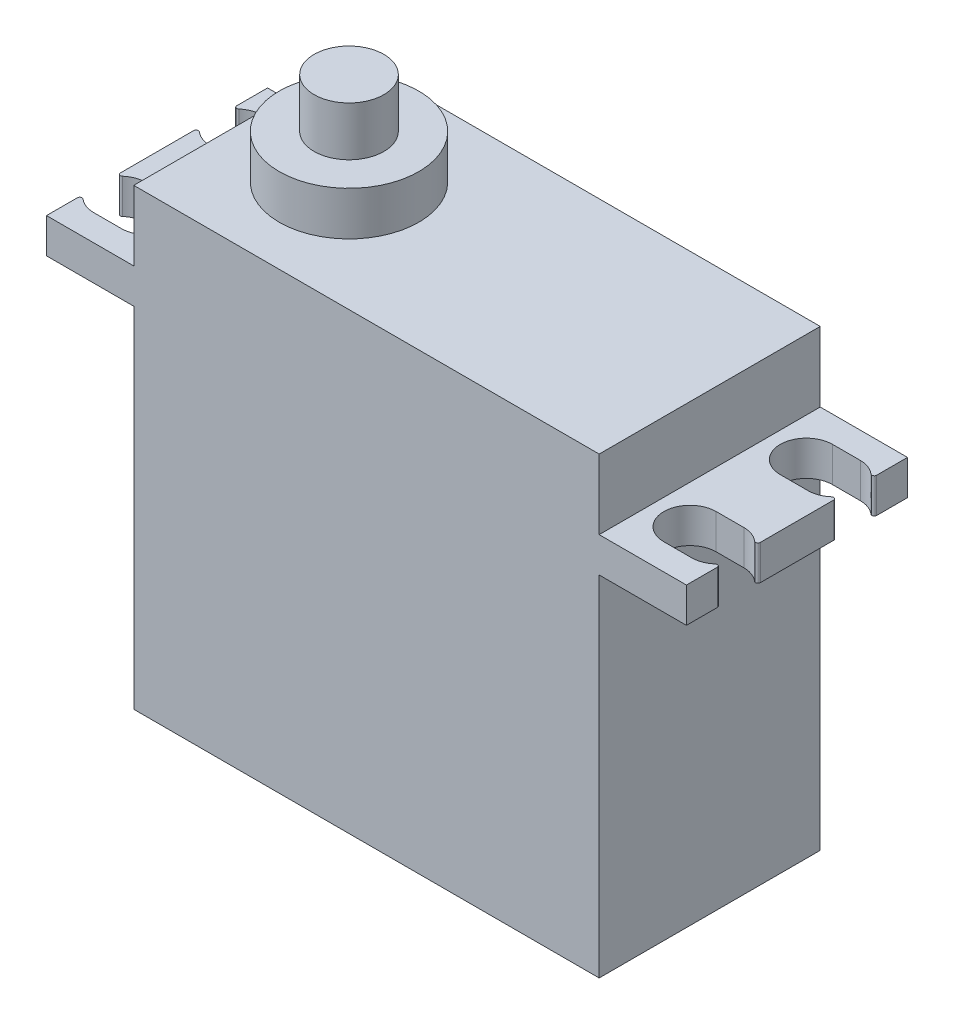
SolidWorks part; units mm, degrees
ref_plane "Front Plane" through (0, 0, 0) normal (0, 0, 1) x (1, 0, 0)
ref_plane "Top Plane" through (0, 0, 0) normal (0, 1, 0) x (1, 0, 0)
ref_plane "Right Plane" through (0, 0, 0) normal (1, 0, 0) x (0, 0, -1)
sketch "Sketch1" plane through (0, 0, 0) normal (0, 1, 0) x (1, 0, 0)
  line L1 (-20, 9.5) -> (20, 9.5)
  line L2 (-20, 9.5) -> (-20, -9.5)
  line L3 (-20, -9.5) -> (20, -9.5)
  line L4 (20, 9.5) -> (20, -9.5)
  line L5 (-20, 9.5) -> (20, -9.5) construction
  line L6 (-20, -9.5) -> (20, 9.5) construction
  point P0 (0, 0)
  dimension "D1" = 19
  dimension "D2" = 40
extrude "Boss-Extrude1" add sketch "Sketch1" along normal blind 39
sketch "Sketch2" plane through (20, 0, 0) normal (1, 0, 0) x (0, 0, -1)
  line L0 (-9.5, 39) -> (-9.5, 0) construction
  line L1 (-9.5, 33) -> (9.5, 33)
  line L2 (-9.5, 33) -> (-9.5, 30)
  line L3 (-9.5, 30) -> (9.5, 30)
  line L4 (9.5, 33) -> (9.5, 30)
  line L5 (9.5, 39) -> (9.5, 0) construction
  line L6 (-9.5, 0) -> (9.5, 0) construction
  dimension "D1" = 30
  dimension "D2" = 3
extrude "Boss-Extrude2" add sketch "Sketch2" along normal blind 7.5 and the other way offset from surface (47.5 mm away) 7.5 other way up to face at (-20, 19.5, 0)
sketch "Sketch3" plane through (0, 33, 0) normal (0, 1, 0) x (1, 0, 0)
  line L0 (0, 9.5) -> (0, -9.5) construction
  line L1 (20, 9.5) -> (-20, 9.5) construction
  line L2 (-20, -9.5) -> (20, -9.5) construction
  line L3 (-24.5, 9.5) -> (-24.5, -9.5) construction
  line L4 (-27.5, 9.5) -> (-20, 9.5) construction
  line L5 (-27.5, -9.5) -> (-20, -9.5) construction
  line L6 (-20, 9.5) -> (-20, -9.5) construction
  line L7 (-23.3097, 5) -> (-25.6903, 5) construction
  line L8 (-23.3097, 2.75) -> (-25.6903, 2.75)
  line L9 (-23.3097, 7.25) -> (-25.6903, 7.25)
  line L10 (-27.5, 0) -> (-20, 0) construction
  line L11 (-27.5, -9.5) -> (-27.5, 9.5) construction
  line L12 (-23.3097, -5) -> (-25.6903, -5) construction
  line L13 (-23.3097, -2.75) -> (-25.6903, -2.75)
  line L14 (-23.3097, -7.25) -> (-25.6903, -7.25)
  line L15 (23.3097, -5) -> (25.6903, -5) construction
  line L16 (23.3097, -2.75) -> (25.6903, -2.75)
  line L17 (23.3097, -7.25) -> (25.6903, -7.25)
  line L18 (23.3097, 5) -> (25.6903, 5) construction
  line L19 (23.3097, 2.75) -> (25.6903, 2.75)
  line L20 (23.3097, 7.25) -> (25.6903, 7.25)
  arc A0 (-23.3097, 2.75) -> (-23.3097, 7.25) centre (-23.3097, 5) ccw
  arc A1 (-25.6903, 7.25) -> (-25.6903, 2.75) centre (-25.6903, 5) ccw
  arc A2 (-23.3097, -2.75) -> (-23.3097, -7.25) centre (-23.3097, -5) cw
  arc A3 (-25.6903, -7.25) -> (-25.6903, -2.75) centre (-25.6903, -5) cw
  arc A4 (23.3097, -2.75) -> (23.3097, -7.25) centre (23.3097, -5) ccw
  arc A5 (25.6903, -7.25) -> (25.6903, -2.75) centre (25.6903, -5) ccw
  arc A6 (23.3097, 2.75) -> (23.3097, 7.25) centre (23.3097, 5) cw
  arc A7 (25.6903, 7.25) -> (25.6903, 2.75) centre (25.6903, 5) cw
  point P16 (-24.5, 5)
  point P23 (-24.5, -5)
  point P34 (24.5, -5)
  point P41 (24.5, 5)
  dimension "D1" = 4.5
  dimension "D2" = 4.5
  dimension "D3" = 5
extrude "Cut-Extrude1" cut sketch "Sketch3" against normal up to surface (3 mm away) up to face at (-23.75, 30, 0)
fillet "Fillet1" radius 0.2 8 edges at (27.5, 31.5, 3.663) (27.5, 31.5, 6.337) (27.5, 31.5, -6.337) (27.5, 31.5, -3.663) (-27.5, 31.5, 3.663) (-27.5, 31.5, 6.337) (-27.5, 31.5, -6.337) (-27.5, 31.5, -3.663)
sketch "Sketch4" plane through (0, 39, 0) normal (0, 1, 0) x (1, 0, 0)
  line L0 (-20, 0) -> (20, 0) construction
  line L1 (-20, 9.5) -> (-20, -9.5) construction
  line L2 (20, -9.5) -> (20, 9.5) construction
  line L3 (-11, 9.5) -> (-11, -9.5) construction
  line L4 (20, 9.5) -> (-20, 9.5) construction
  line L5 (-20, -9.5) -> (20, -9.5) construction
  line L6 (-20, 9.5) -> (-20, -9.5) construction
  circle A0 centre (-11, 0) radius 3
  dimension "D2" = 6
  dimension "D1" = 9
extrude "Boss-Extrude3" add sketch "Sketch4" along normal blind 8
sketch "Sketch6" plane through (0, 39, 0) normal (0, 1, 0) x (1, 0, 0)
  circle A0 centre (-11, 0) radius 6
  dimension "D1" = 12
extrude "Boss-Extrude4" add sketch "Sketch6" along normal blind 3.77
